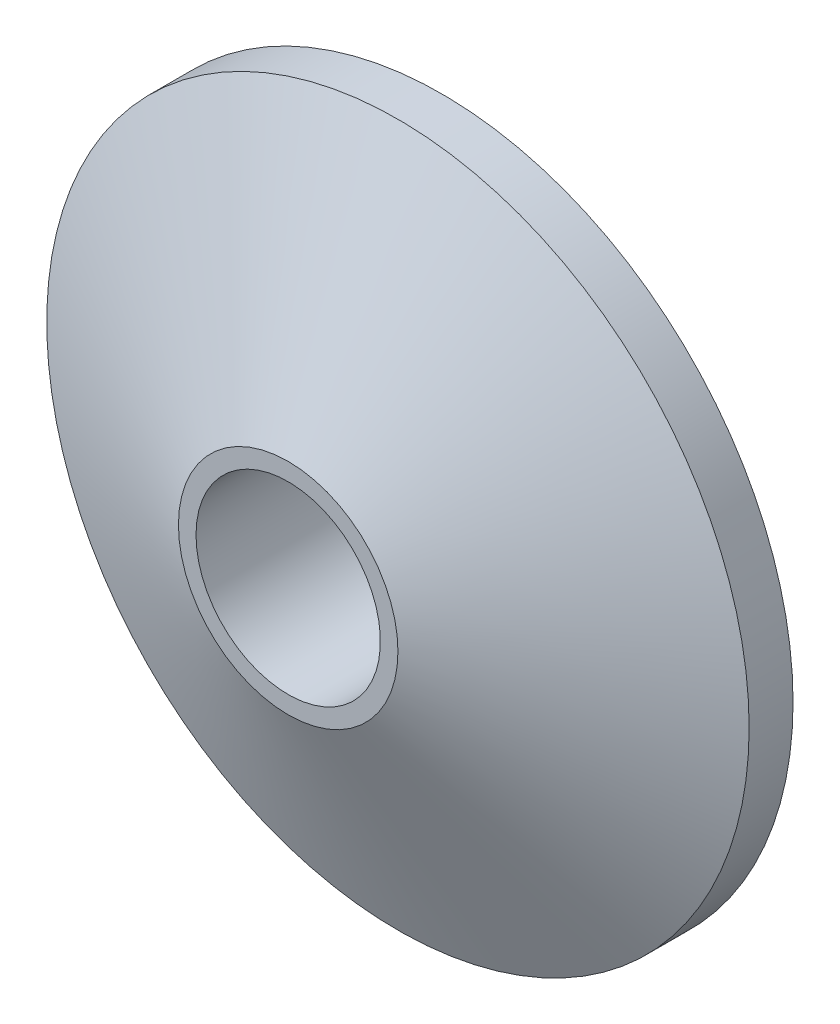
SolidWorks part; units mm, degrees
ref_plane "Front Plane" through (0, 0, 0) normal (0, 0, 1) x (1, 0, 0)
ref_plane "Top Plane" through (0, 0, 0) normal (0, 1, 0) x (1, 0, 0)
ref_plane "Right Plane" through (0, 0, 0) normal (1, 0, 0) x (0, 0, -1)
sketch "Sketch1" plane through (0, 0, 0) normal (0, 0, 1) x (1, 0, 0)
  circle A0 centre (0, 0) radius 8
  dimension "D1" = 16
extrude "Boss-Extrude1" add sketch "Sketch1" along normal blind 3.5
chamfer "Chamfer1" distance 2.5 distance2 5.5 1 edges at (8, 0, 3.5)
hole_wizard "Tap Drill for M5x0.8 Tap1" positions "Sketch4" profile "Sketch3" hole size "M5x0.8" standard "Ansi Metric" end condition through all
sketch "Sketch4" plane through (0, 0, 0) normal (0, 0, -1) x (-1, 0, 0)
  circle A0 centre (0, 0) radius 8 construction
  point P0 (0, 0)
sketch "Sketch3" plane through (0, 0, 0) normal (1, 0, 0) x (0, 1, 0)
  line L0 (0, 0) -> (0, 3.5)
  line L1 (0, 3.5) -> (2.1, 3.5)
  line L2 (2.1, 3.5) -> (2.1, 0)
  line L5 (2.1, 0) -> (0, 0)
  line L11 (0, -6.35) -> (0, 107.95) construction
  dimension "Thru Hole Dia." = 4.2
  dimension "Thru Hole Depth" = 3.5
